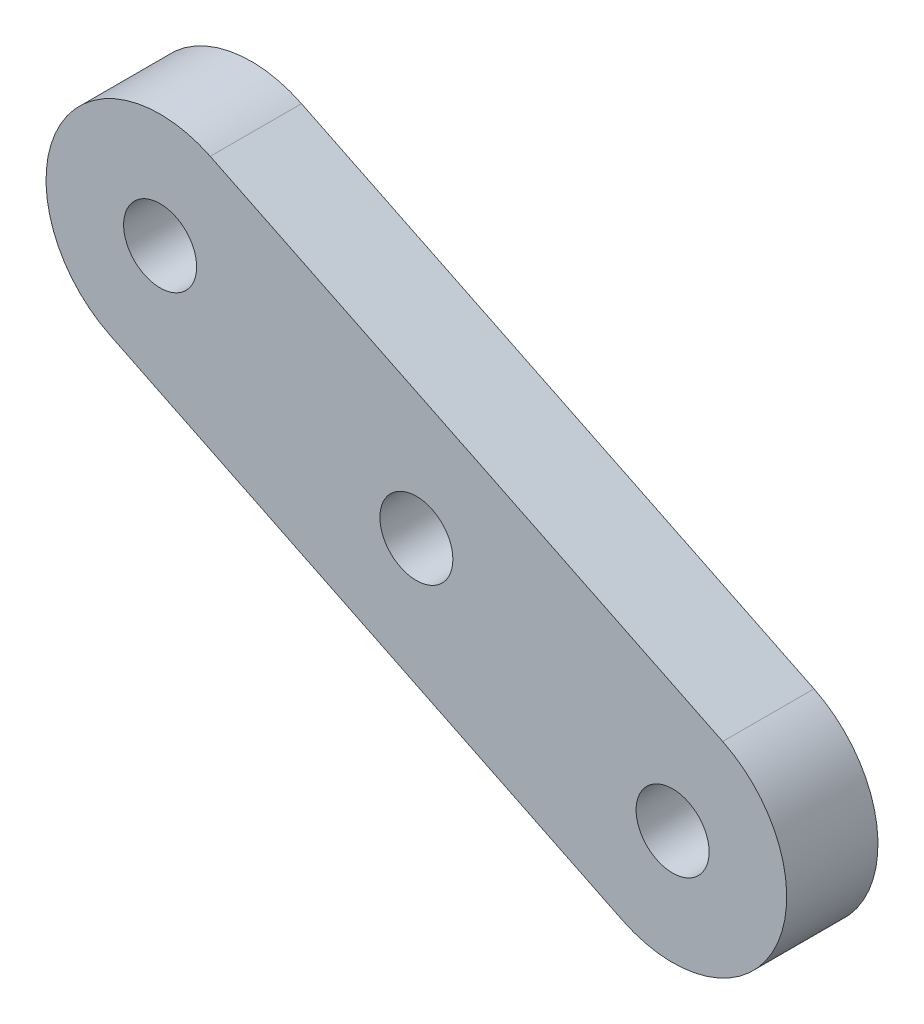
SolidWorks part; units mm, degrees
ref_plane "Front Plane" through (0, 0, 0) normal (0, 0, 1) x (1, 0, 0)
ref_plane "Top Plane" through (0, 0, 0) normal (0, 1, 0) x (1, 0, 0)
ref_plane "Right Plane" through (0, 0, 0) normal (1, 0, 0) x (0, 0, -1)
sketch "Sketch1" plane through (0, 0, 0) normal (0, 0, 1) x (1, 0, 0)
  line L0 (0, 0) -> (-22.4605, 10.9784) construction
  line L1 (-2.1957, -4.4921) -> (-24.6562, 6.4863)
  line L2 (2.1957, 4.4921) -> (-20.2648, 15.4705)
  arc A0 (-2.1957, -4.4921) -> (2.1957, 4.4921) centre (0, 0) ccw
  arc A1 (-20.2648, 15.4705) -> (-24.6562, 6.4863) centre (-22.4605, 10.9784) ccw
  circle A2 centre (-22.4605, 10.9784) radius 1.6
  circle A3 centre (0, 0) radius 1.6
  circle A4 centre (-11.2302, 5.4892) radius 1.6
  point P3 (-11.2302, 5.4892)
  dimension "D3" = 3.2
  dimension "D1" = 10
  dimension "D2" = 25
extrude "Boss-Extrude1" add sketch "Sketch1" along normal blind 4
